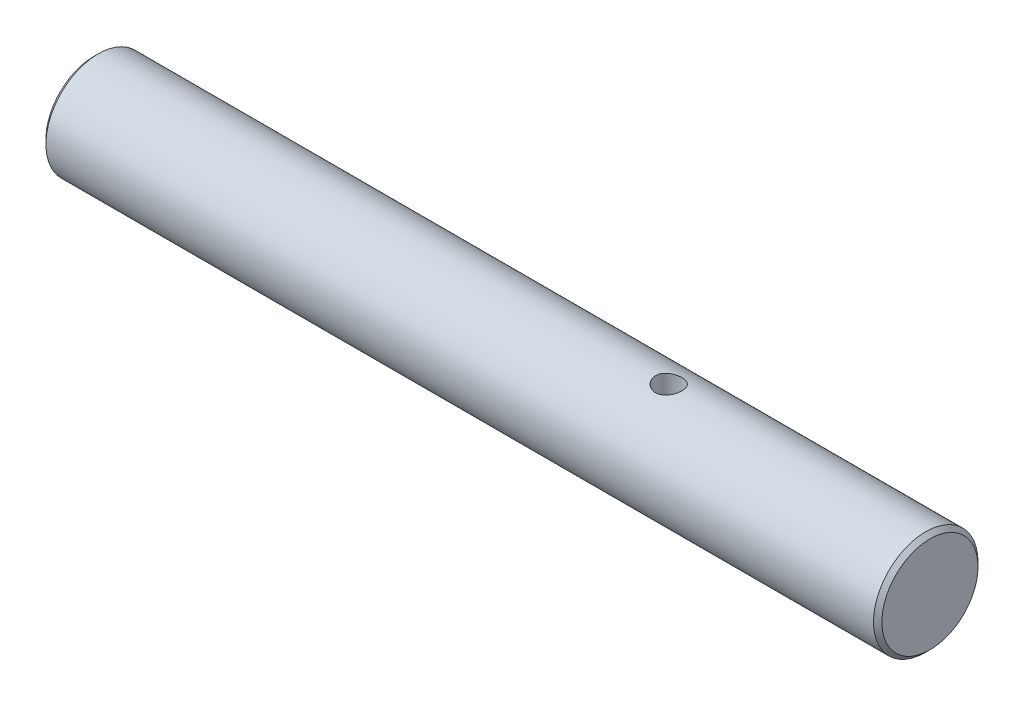
SolidWorks part; units mm, degrees
ref_plane "Front Plane" through (0, 0, 0) normal (0, 0, 1) x (1, 0, 0)
ref_plane "Top Plane" through (0, 0, 0) normal (0, 1, 0) x (1, 0, 0)
ref_plane "Right Plane" through (0, 0, 0) normal (1, 0, 0) x (0, 0, -1)
sketch "Sketch1" plane through (0, 0, 0) normal (1, 0, 0) x (0, 0, -1)
  circle A0 centre (0, 0) radius 3.175
  dimension "D1" = 6.35
extrude "Boss-Extrude1" add sketch "Sketch1" against normal blind 50.8
chamfer "Chamfer1" distance 0.254 angle 45 2 edges at (-50.8, 0, -3.175) (0, 0, -3.175)
sketch "Sketch2" plane through (0, 0, 0) normal (0, 1, 0) x (1, 0, 0)
  line L0 (0, -2.921) -> (0, 2.921) construction
  circle A0 centre (-15.875, 0) radius 0.8001
  dimension "D2" = 1.6002
  dimension "D1" = 15.875
extrude "Cut-Extrude1" cut sketch "Sketch2" against normal through all and the other way through all
